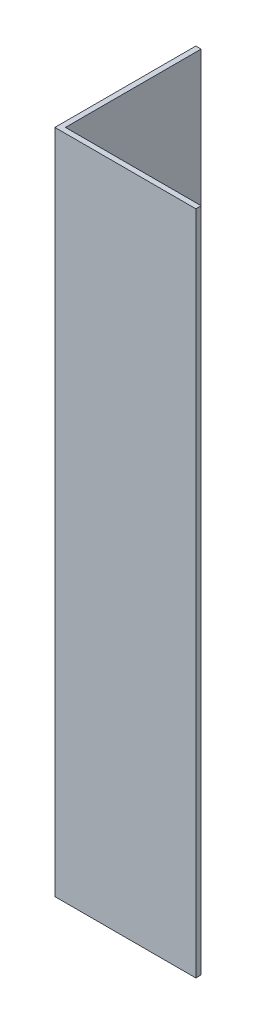
SolidWorks part; units mm, degrees
material "1060 Сплав"
ref_plane "Спереди" through (0, 0, 0) normal (0, 0, 1) x (1, 0, 0)
ref_plane "Сверху" through (0, 0, 0) normal (0, 1, 0) x (1, 0, 0)
ref_plane "Справа" through (0, 0, 0) normal (1, 0, 0) x (0, 0, -1)
sketch "Эскиз1" plane through (0, 0, 0) normal (0, 1, 0) x (1, 0, 0)
  line L0 (0, 0) -> (0, 20)
  line L1 (0, 20) -> (0.75, 20)
  line L2 (0.75, 20) -> (0.75, 0.75)
  line L3 (0.75, 0.75) -> (20, 0.75)
  line L4 (20, 0.75) -> (20, 0)
  line L5 (20, 0) -> (0, 0)
  dimension "D1" = 0.75
  dimension "D2" = 20
extrude "Бобышка-Вытянуть1" add sketch "Эскиз1" along normal blind 94.5
sketch "Эскиз2" plane through (0, 0, -0.75) normal (0, 0, -1) x (-1, 0, 0)
  line L0 (-20, 47.25) -> (-0.75, 47.25) construction
  line L1 (-20, 94.5) -> (-20, 0) construction
  line L2 (-0.75, 94.5) -> (-0.75, 0) construction
